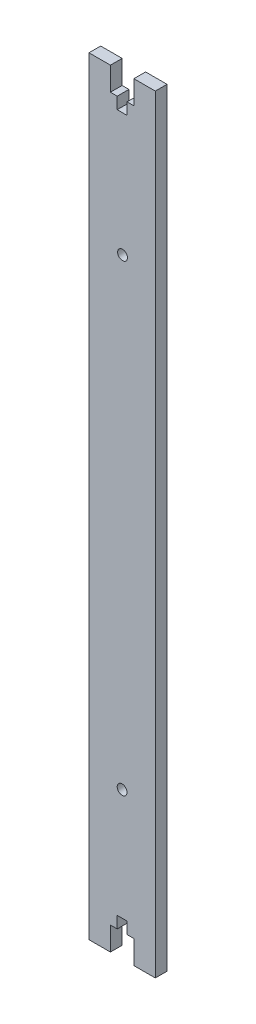
SolidWorks part; units mm, degrees
ref_plane "Front Plane" through (0, 0, 0) normal (0, 0, 1) x (1, 0, 0)
ref_plane "Top Plane" through (0, 0, 0) normal (0, 1, 0) x (1, 0, 0)
ref_plane "Right Plane" through (0, 0, 0) normal (1, 0, 0) x (0, 0, -1)
sketch "Sketch1" plane through (0, 0, 0) normal (0, 0, 1) x (1, 0, 0)
  line L1 (-14.14, 163.75) -> (14.14, 163.75)
  line L2 (-14.14, 163.75) -> (-14.14, -163.75)
  line L3 (-14.14, -163.75) -> (14.14, -163.75)
  line L4 (14.14, 163.75) -> (14.14, -163.75)
  line L5 (-14.14, 163.75) -> (14.14, -163.75) construction
  line L6 (-14.14, -163.75) -> (14.14, 163.75) construction
  point P0 (0, 0)
  dimension "D1" = 327.5
  dimension "D2" = 28.28
extrude "Boss-Extrude1" add sketch "Sketch1" along normal blind 5
sketch "Sketch2" plane through (0, 0, 5) normal (0, 0, 1) x (1, 0, 0)
  line L0 (0, 163.75) -> (0, 146.1036) construction
  line L1 (14.14, 163.75) -> (-14.14, 163.75) construction
  line L2 (14.14, 0) -> (0, 0) construction
  line L3 (14.14, -163.75) -> (14.14, 163.75) construction
  line L4 (5, 163.75) -> (5, 153.75)
  line L5 (5, 153.75) -> (2.1, 153.75)
  line L6 (2.1, 153.75) -> (2.1, 148.75)
  line L7 (2.1, 148.75) -> (-2.1, 148.75)
  line L8 (5, 163.75) -> (-5, 163.75)
  line L9 (-2.1, 153.75) -> (-2.1, 148.75)
  line L10 (-5, 153.75) -> (-2.1, 153.75)
  line L11 (-5, 163.75) -> (-5, 153.75)
  line L12 (-5, -163.75) -> (-5, -153.75)
  line L13 (-5, -153.75) -> (-2.1, -153.75)
  line L14 (-2.1, -153.75) -> (-2.1, -148.75)
  line L15 (5, -163.75) -> (-5, -163.75)
  line L16 (2.1, -148.75) -> (-2.1, -148.75)
  line L17 (2.1, -153.75) -> (2.1, -148.75)
  line L18 (5, -153.75) -> (2.1, -153.75)
  line L19 (5, -163.75) -> (5, -153.75)
  line L20 (-15.9334, 96.25) -> (16.2613, 96.25) construction
  line L21 (-15.9334, 93.75) -> (-15.9334, 98.75) construction
  line L22 (16.2613, 93.75) -> (16.2613, 98.75) construction
  circle A0 centre (0.164, 96.25) radius 2.1
  point P16 (0, 148.75)
  point P26 (0, -148.75)
  dimension "D5" = 4.2
  dimension "D1" = 5
  dimension "D2" = 10
  dimension "D3" = 2.9
  dimension "D4" = 5
extrude "Cut-Extrude1" cut sketch "Sketch2" against normal blind 10
sketch "Sketch3" plane through (0, 0, 5) normal (0, 0, 1) x (1, 0, 0)
  line L0 (-14.1443, -101.25) -> (14.14, -101.25) construction
  line L1 (-14.1443, -103.75) -> (-14.1443, -98.75) construction
  line L2 (14.14, -103.75) -> (14.14, -98.75) construction
  circle A0 centre (-0.0021, -101.25) radius 2.1
  dimension "D1" = 4.2
extrude "Cut-Extrude2" cut sketch "Sketch3" against normal blind 10
